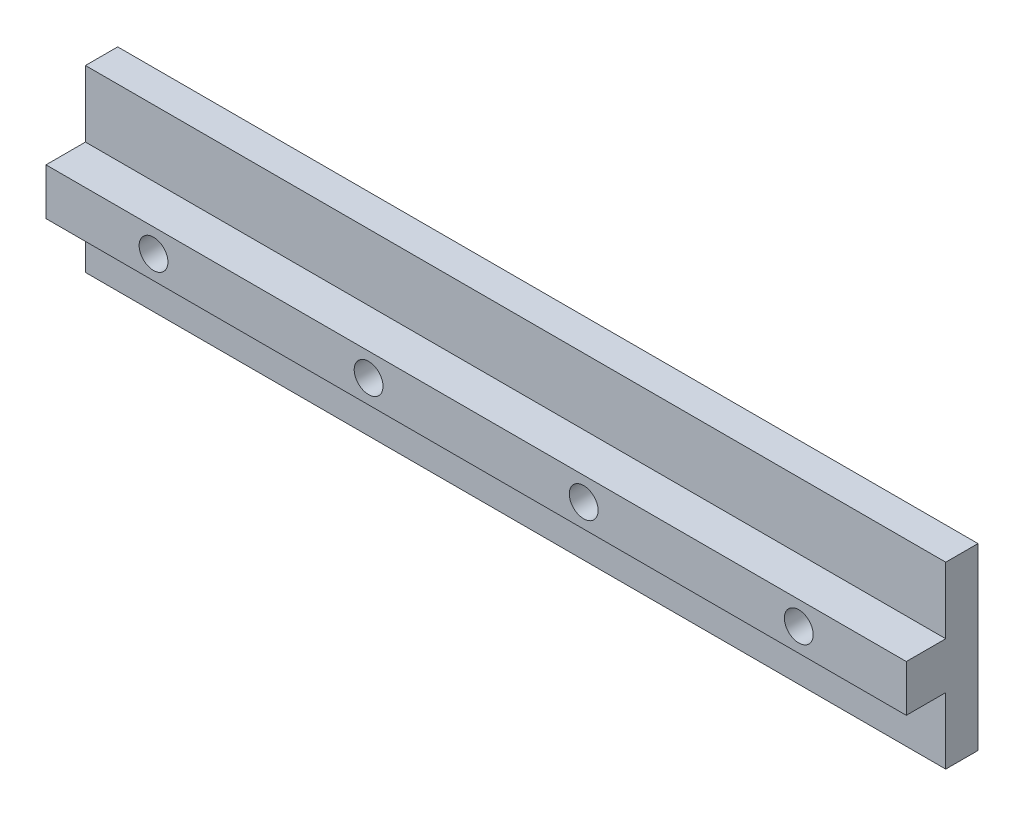
SolidWorks part; units mm, degrees
ref_plane "Front Plane" through (0, 0, 0) normal (0, 0, 1) x (1, 0, 0)
ref_plane "Top Plane" through (0, 0, 0) normal (0, 1, 0) x (1, 0, 0)
ref_plane "Right Plane" through (0, 0, 0) normal (1, 0, 0) x (0, 0, -1)
sketch "Sketch1" plane through (0, 0, 0) normal (0, 0, 1) x (1, 0, 0)
  line L1 (-76.2, 15.875) -> (76.2, 15.875)
  line L2 (-76.2, 15.875) -> (-76.2, -15.875)
  line L3 (-76.2, -15.875) -> (76.2, -15.875)
  line L4 (76.2, 15.875) -> (76.2, -15.875)
  line L5 (-76.2, 15.875) -> (76.2, -15.875) construction
  line L6 (-76.2, -15.875) -> (76.2, 15.875) construction
  point P0 (0, 0)
  dimension "D1" = 152.4
  dimension "D2" = 31.75
extrude "Boss-Extrude1" add sketch "Sketch1" along normal blind 12.7
sketch "Sketch2" plane through (0, 0, 12.7) normal (0, 0, 1) x (1, 0, 0)
  line L0 (76.2, -15.875) -> (76.2, 15.875) construction
  line L1 (-76.2, 15.875) -> (76.2, 15.875)
  line L2 (-76.2, 15.875) -> (-76.2, 4.1275)
  line L3 (-76.2, 4.1275) -> (76.2, 4.1275)
  line L4 (76.2, 15.875) -> (76.2, 4.1275)
  line L5 (0, 4.1275) -> (0, -4.1275) construction
  line L6 (-76.2, -15.875) -> (76.2, -15.875)
  line L7 (-76.2, -15.875) -> (-76.2, -4.1275)
  line L8 (-76.2, -4.1275) -> (76.2, -4.1275)
  line L9 (76.2, -15.875) -> (76.2, -4.1275)
  dimension "D1" = 8.255
extrude "Cut-Extrude1" cut sketch "Sketch2" against normal blind 6.985
hole_wizard "1/4-20 Tapped Hole1" positions "Sketch4" profile "Sketch3" tap size "1/4-20" standard "ANSI Inch" end condition up to next
sketch "Sketch4" plane through (0, 0, 12.7) normal (0, 0, 1) x (1, 0, 0)
  line L0 (57.15, 0) -> (19.05, 0) construction
  line L1 (19.05, 0) -> (-19.05, 0) construction
  line L2 (-19.05, 0) -> (-57.15, 0) construction
  line L3 (57.15, 0) -> (76.2, 0) construction
  line L4 (76.2, -4.1275) -> (76.2, 4.1275) construction
  point P0 (-57.15, 0)
  point P2 (-19.05, 0)
  point P4 (19.05, 0)
  point P6 (57.15, 0)
  dimension "D1" = 38.1
  dimension "D2" = 38.1
  dimension "D3" = 38.1
sketch "Sketch3" plane through (-57.15, 0, 12.7) normal (1, 0, 0) x (0, -1, 0)
  line L0 (0, 0) -> (0, 12.7)
  line L1 (0, 12.7) -> (2.5527, 12.7)
  line L2 (2.5527, 12.7) -> (2.5527, 0)
  line L5 (2.5527, 0) -> (0, 0)
  line L11 (0, -6.35) -> (0, 107.95) construction
  dimension "Thread Major Dia." = 5.1054
  dimension "Thru Tap Drill Depth" = 12.7
